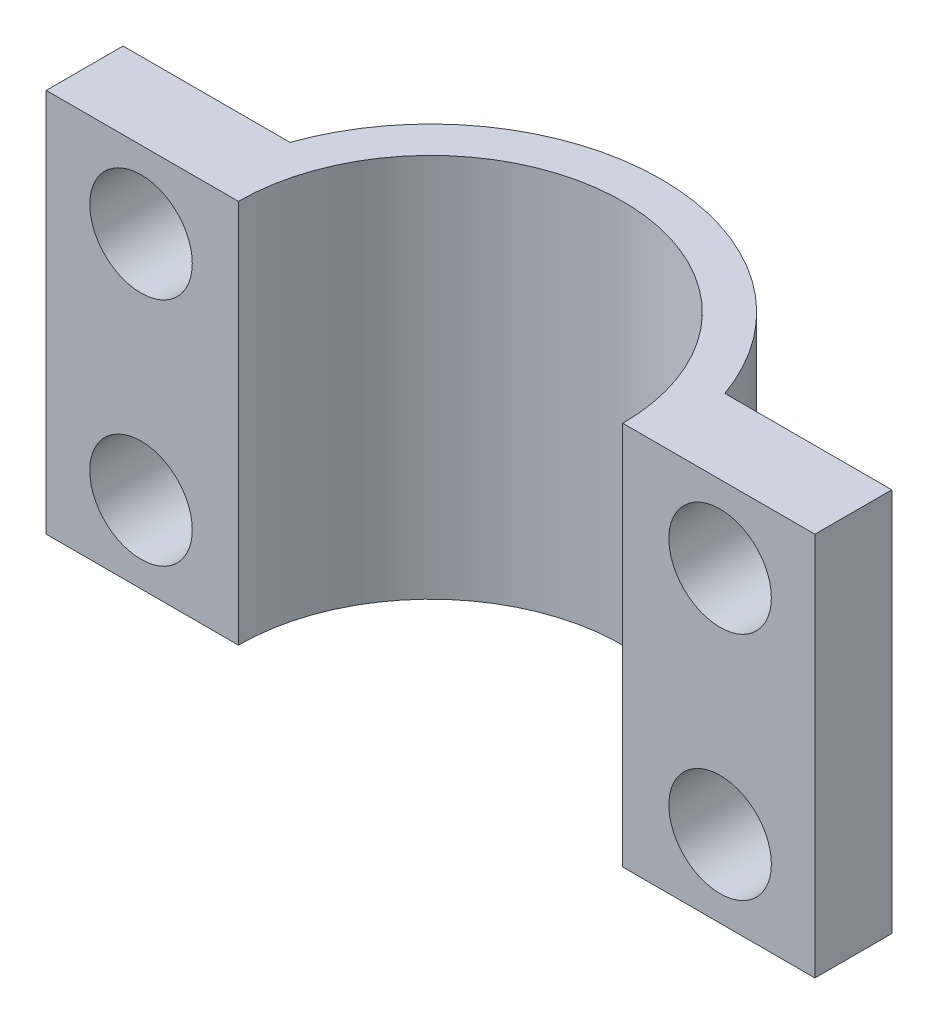
SolidWorks part; units mm, degrees
ref_plane "Front Plane" through (0, 0, 0) normal (0, 0, 1) x (1, 0, 0)
ref_plane "Top Plane" through (0, 0, 0) normal (0, 1, 0) x (1, 0, 0)
ref_plane "Right Plane" through (0, 0, 0) normal (1, 0, 0) x (0, 0, -1)
sketch "Sketch1" plane through (0, 0, 0) normal (0, 0, 1) x (1, 0, 0)
  line L1 (15, -7.5) -> (-15, -7.5)
  line L2 (15, -7.5) -> (15, 7.5)
  line L3 (15, 7.5) -> (-15, 7.5)
  line L4 (-15, -7.5) -> (-15, 7.5)
  line L5 (15, -7.5) -> (-15, 7.5) construction
  line L6 (15, 7.5) -> (-15, -7.5) construction
  point P0 (0, 0)
  dimension "D1" = 30
  dimension "D2" = 15
extrude "Boss-Extrude1" add sketch "Sketch1" along normal blind 15
sketch "Sketch2" plane through (0, -7.5, 0) normal (0, -1, 0) x (1, 0, 0)
  line L0 (-15, 15) -> (15, 15) construction
  line L1 (-15, 12) -> (-9, 12)
  line L2 (-9, 12) -> (-8.4853, 12)
  line L3 (-15, 15) -> (-15, 0) construction
  line L5 (8.4853, 12) -> (9, 12)
  line L6 (-15, 0) -> (15, 0) construction
  line L7 (-11, 0) -> (-15, 0)
  line L8 (-15, 0) -> (-15, 12)
  line L9 (0, 15) -> (0, 4.1396) construction
  line L10 (11, 0) -> (15, 0)
  line L11 (15, 12) -> (9, 12)
  line L12 (15, 0) -> (15, 12)
  line L13 (-11, 0) -> (11, 0)
  circle A0 centre (0, 15) radius 7.5
  arc A1 (-8.4853, 12) -> (8.4853, 12) centre (0, 15) ccw
  dimension "D1" = 15
  dimension "D2" = 9
  dimension "D3" = 9
  dimension "D4" = 12
extrude "Cut-Extrude1" cut sketch "Sketch2" against normal blind 15
sketch "Sketch3" plane through (0, 0, 12) normal (0, 0, -1) x (-1, 0, 0)
  line L0 (0, 0) -> (0, -9.8306) construction
  line L2 (8.4853, 7.5) -> (15, 7.5) construction
  line L3 (8.4853, -7.5) -> (15, -7.5) construction
  circle A0 centre (11.3, -4.5) radius 2
  circle A1 centre (11.3, 4.5) radius 2
  circle A2 centre (-11.3, 4.5) radius 2
  circle A3 centre (-11.3, -4.5) radius 2
  point P9 (10.8112, 7.5)
  dimension "D1" = 4
  dimension "D2" = 4
  dimension "D3" = 11.3
  dimension "D4" = 11.3
  dimension "D5" = 3
  dimension "D6" = 3
extrude "Cut-Extrude2" cut sketch "Sketch3" against normal up to next
